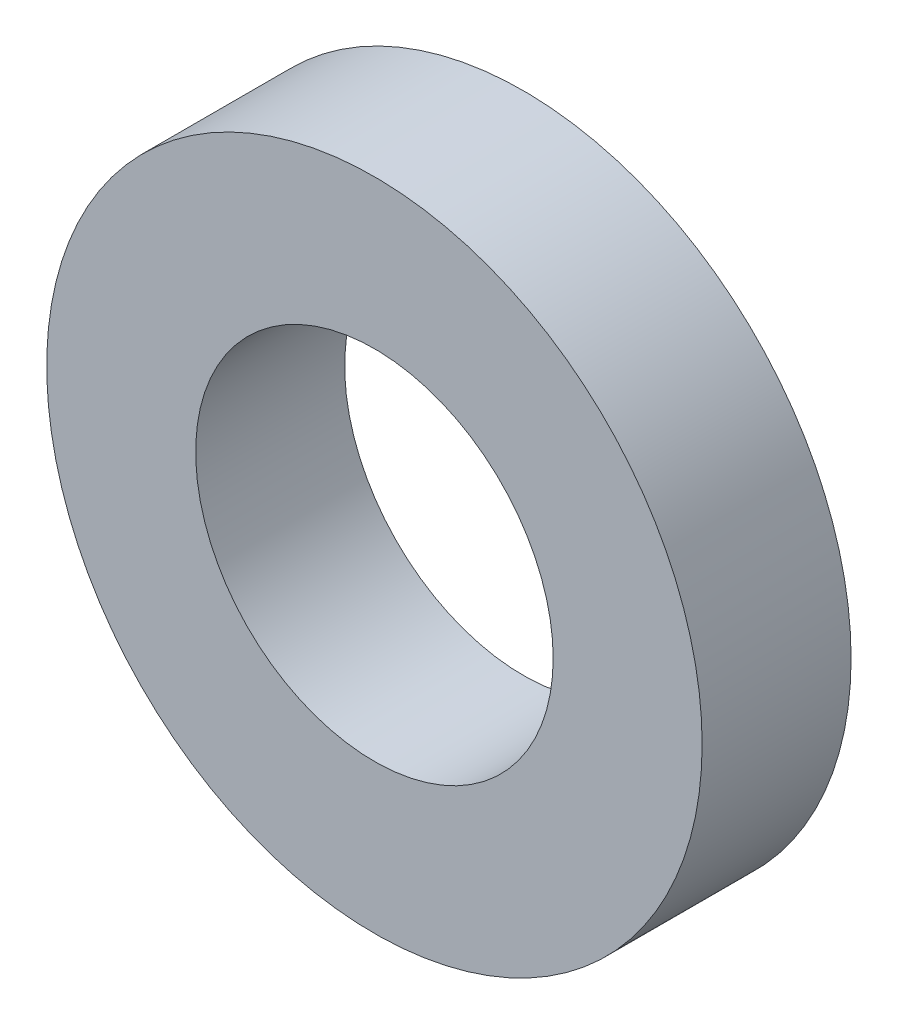
SolidWorks part; units mm, degrees
material "Резина"
ref_plane "Спереди" through (0, 0, 0) normal (0, 0, 1) x (1, 0, 0)
ref_plane "Сверху" through (0, 0, 0) normal (0, 1, 0) x (1, 0, 0)
ref_plane "Справа" through (0, 0, 0) normal (1, 0, 0) x (0, 0, -1)
sketch "Эскиз1" plane through (0, 0, 0) normal (0, 0, 1) x (1, 0, 0)
  circle A0 centre (0, 0) radius 6
  circle A1 centre (0, 0) radius 11
  dimension "D1" = 12
  dimension "D2" = 22
extrude "Бобышка-Вытянуть1" add sketch "Эскиз1" along normal blind 5
